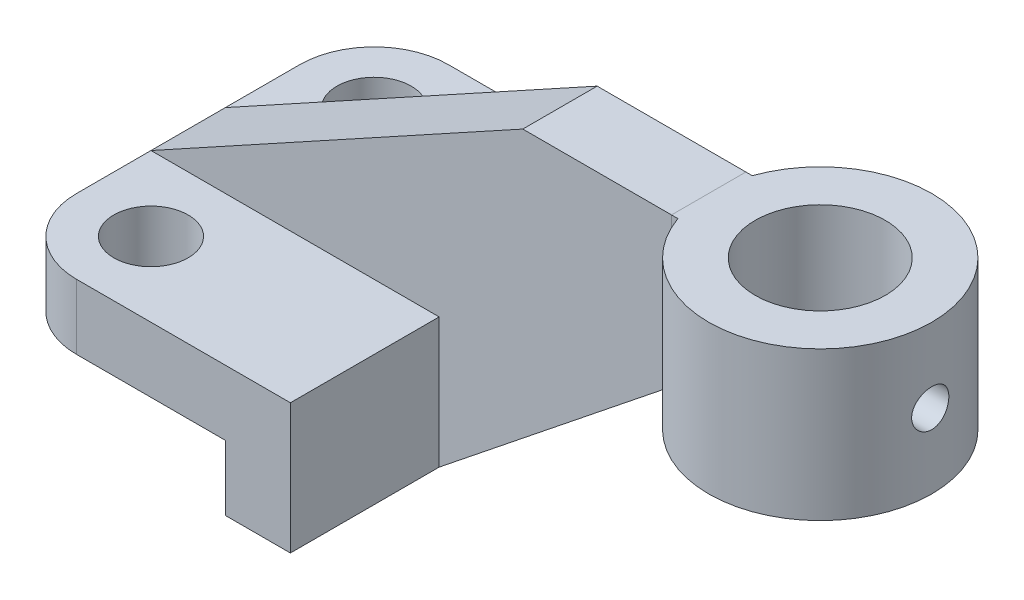
SolidWorks part; units mm, degrees
ref_plane "Alzado" through (0, 0, 0) normal (0, 0, 1) x (1, 0, 0)
ref_plane "Planta" through (0, 0, 0) normal (0, 1, 0) x (1, 0, 0)
ref_plane "Vista lateral" through (0, 0, 0) normal (1, 0, 0) x (0, 0, -1)
sketch "Croquis1" plane through (0, 0, 0) normal (0, 1, 0) x (1, 0, 0)
  line L0 (-63.5, -31.75) -> (-63.5, 31.75)
  line L1 (-63.5, -31.75) -> (63.5, -31.75) construction
  line L2 (-63.5, -31.75) -> (-63.5, 31.75) construction
  line L3 (-63.5, 31.75) -> (63.5, 31.75) construction
  line L4 (63.5, -31.75) -> (63.5, 31.75) construction
  line L5 (-63.5, -31.75) -> (63.5, 31.75) construction
  line L6 (-63.5, 31.75) -> (63.5, -31.75) construction
  line L7 (-63.5, 31.75) -> (-14.2875, 31.75) construction
  line L8 (-14.2875, 31.75) -> (-14.2875, -31.75)
  line L9 (-14.2875, -31.75) -> (-63.5, -31.75) construction
  line L10 (-25.4, 31.75) -> (-50.8, 31.75)
  line L11 (-50.8, 31.75) -> (-50.8, 19.05)
  line L12 (-50.8, 19.05) -> (-50.8, -19.05) construction
  line L13 (-50.8, -31.75) -> (-14.2875, -31.75)
  line L14 (-14.2875, 31.75) -> (-25.4, 31.75)
  line L15 (-25.4, 31.75) -> (-25.4, -31.75)
  line L16 (-25.4, -31.75) -> (-14.2875, -31.75)
  arc A0 (-63.5, 19.05) -> (-50.8, 31.75) centre (-50.8, 19.05) cw
  arc A1 (-63.5, -19.05) -> (-50.8, -31.75) centre (-50.8, -19.05) ccw
  circle A2 centre (-50.8, 19.05) radius 6.35
  circle A3 centre (-50.8, -19.05) radius 6.35
  point P0 (0, 0)
  dimension "D7" = 12.7
  dimension "D8" = 12.7
  dimension "D9" = 11.1125
  dimension "D1" = 127
  dimension "D2" = 63.5
  dimension "D3" = 49.2125
  dimension "D4" = 25.4
  dimension "D5" = 12.7
  dimension "D6" = 38.1
extrude "Saliente-Extruir3" add sketch "Croquis1" against normal blind 11.1125
sketch "Croquis3" plane through (0, -11.1125, 0) normal (0, -1, 0) x (1, 0, 0)
  line L0 (-14.2875, 31.75) -> (-14.2875, -31.75)
  line L1 (-14.2875, -31.75) -> (-25.4, -31.75)
  line L2 (-14.2875, -31.75) -> (-50.8, -31.75) construction
  line L3 (-25.4, -31.75) -> (-25.4, 31.75)
  line L4 (-50.8, 31.75) -> (-14.2875, 31.75) construction
  line L5 (-25.4, 31.75) -> (-14.2875, 31.75)
  dimension "D1" = 11.1125
extrude "Saliente-Extruir4" add sketch "Croquis3" along normal blind 11.1125
sketch "Croquis4" plane through (0, 0, 0) normal (0, 0, 1) x (1, 0, 0)
  line L0 (-63.5, 0) -> (0, 34.925)
  line L1 (-14.2875, -22.225) -> (25.4, 9.525)
  line L2 (-14.2875, -22.225) -> (0, -22.225) construction
  line L3 (0, -22.225) -> (0, 34.925) construction
  line L4 (25.4, 9.525) -> (25.4, -22.225) construction
  line L5 (25.4, -22.225) -> (-14.2875, -22.225) construction
  line L6 (0, 34.925) -> (25.4, 34.925)
  line L7 (25.4, 34.925) -> (25.4, 9.525)
  line L8 (25.4, 34.925) -> (63.5, 34.925)
  line L9 (63.5, 34.925) -> (63.5, 9.525)
  line L10 (63.5, 9.525) -> (25.4, 9.525)
  line L11 (25.4, 34.925) -> (63.5, 34.925)
  line L12 (25.4, 9.525) -> (63.5, 9.525)
  line L13 (-63.5, 0) -> (-14.2875, 0)
  line L14 (-14.2875, 0) -> (-14.2875, -22.225)
  dimension "D1" = 14.2875
  dimension "D2" = 57.15
  dimension "D3" = 39.6875
  dimension "D4" = 31.75
  dimension "D5" = 38.1
extrude "Saliente-Extruir5" add sketch "Croquis4" along normal mid plane 12.7 contours L13 L14 L1 L7 L6 L0
ref_plane "Plano2" through (0, 34.925, 0) normal (0, 1, 0) x (1, 0, 0)
sketch "Croquis6" plane through (0, 34.925, 0) normal (0, 1, 0) x (1, 0, 0)
  line L0 (25.4, 0) -> (63.5, 0) construction
  line L1 (25.4, -6.35) -> (25.4, 6.35) construction
  line L2 (25.4, 6.35) -> (26.4895, 6.35)
  line L3 (25.4, -6.35) -> (26.4895, -6.35)
  line L4 (25.4, 6.35) -> (25.4, -6.35)
  arc A0 (26.4895, -6.35) -> (26.4895, 6.35) centre (44.45, 0) ccw
  circle A1 centre (44.45, 0) radius 11.1125
  dimension "D2" = 22.225
  dimension "D3" = 19.05
  dimension "D1" = 38.1
extrude "Saliente-Extruir6" add sketch "Croquis6" against normal blind 25.4 separate body
ref_plane "Plano3" through (63.5, 0, 0) normal (1, 0, 0) x (0, 0, -1)
sketch "Croquis7" plane through (63.5, 0, 0) normal (1, 0, 0) x (0, 0, -1)
  line L0 (0, 34.925) -> (0, 22.225) construction
  line L1 (32.0014, 34.925) -> (-32.0014, 34.925) construction
  circle A0 centre (0, 22.225) radius 3.175
  dimension "D2" = 6.35
  dimension "D1" = 12.7
extrude "Cortar-Extruir2" cut sketch "Croquis7" against normal blind 19.05
